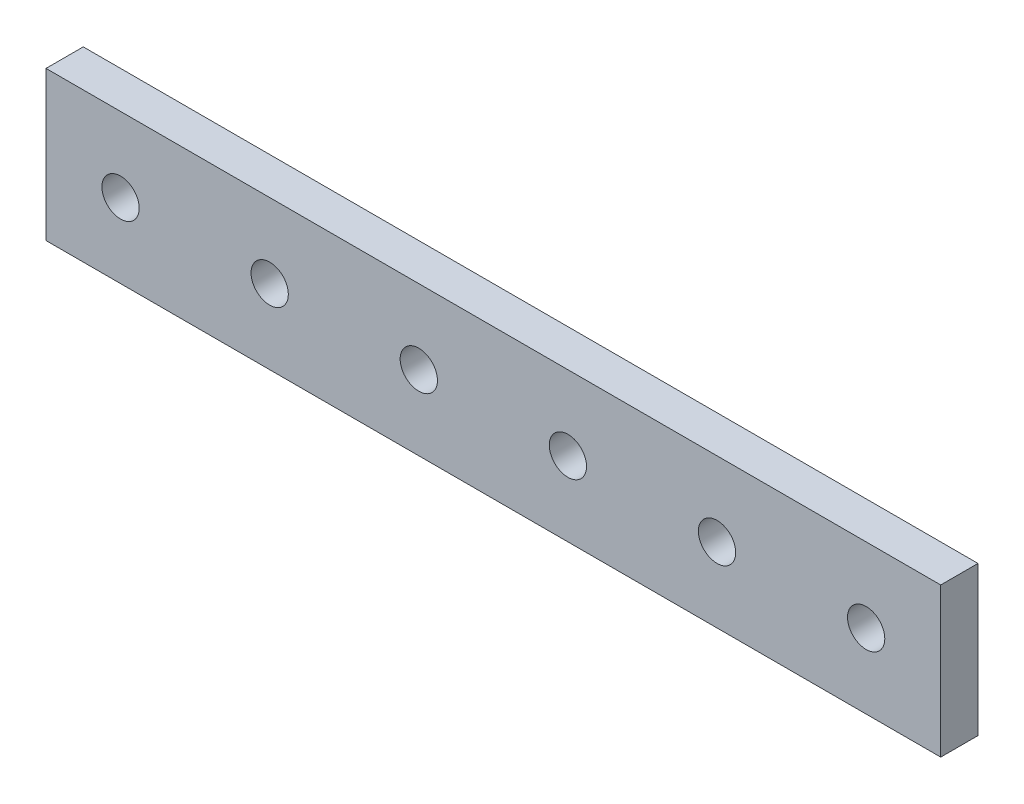
SolidWorks part; units mm, degrees
ref_plane "Front Plane" through (0, 0, 0) normal (0, 0, 1) x (1, 0, 0)
ref_plane "Top Plane" through (0, 0, 0) normal (0, 1, 0) x (1, 0, 0)
ref_plane "Right Plane" through (0, 0, 0) normal (1, 0, 0) x (0, 0, -1)
sketch "Sketch1" plane through (0, 0, 0) normal (0, 0, 1) x (1, 0, 0)
  line L1 (-76.2, -12.7) -> (76.2, -12.7)
  line L2 (-76.2, -12.7) -> (-76.2, 12.7)
  line L3 (-76.2, 12.7) -> (76.2, 12.7)
  line L4 (76.2, -12.7) -> (76.2, 12.7)
  line L5 (-76.2, -12.7) -> (76.2, 12.7) construction
  line L6 (-76.2, 12.7) -> (76.2, -12.7) construction
  point P0 (0, 0)
  dimension "D1" = 152.4
  dimension "D2" = 25.4
extrude "Boss-Extrude1" add sketch "Sketch1" along normal blind 6.35
sketch "Sketch2" plane through (0, 0, 6.35) normal (0, 0, 1) x (1, 0, 0)
  line L0 (0, 0) -> (-76.2, 0) construction
  line L1 (-76.2, 12.7) -> (-76.2, -12.7) construction
  line L2 (0, 0) -> (76.2, 0) construction
  line L3 (76.2, -12.7) -> (76.2, 12.7) construction
  circle A0 centre (-12.7, 0) radius 3.175
  circle A2 centre (38.1, 0) radius 3.175
  circle A3 centre (63.5, 0) radius 3.175
  circle A4 centre (12.7, 0) radius 3.175
  circle A5 centre (-38.1, 0) radius 3.175
  circle A6 centre (-63.5, 0) radius 3.175
  point P18 (-38.1, 0)
  point P21 (-57.9267, 0)
  dimension "D1" = 6.35
  dimension "D2" = 6.35
  dimension "D3" = 6.35
  dimension "D4" = 25.4
  dimension "D5" = 25.4
  dimension "D6" = 12.7
  dimension "D7" = 6.35
  dimension "D8" = 25.4
  dimension "D9" = 25.4
  dimension "D10" = 6.35
  dimension "D11" = 6.35
extrude "Cut-Extrude1" cut sketch "Sketch2" against normal blind 6.35
